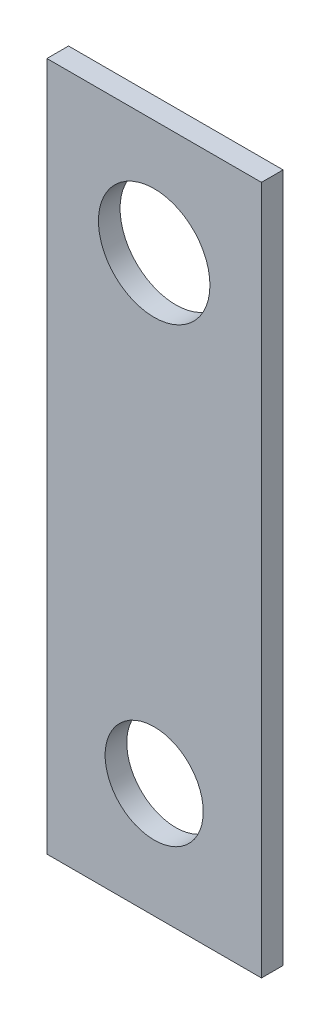
SolidWorks part; units mm, degrees
ref_plane "Front Plane" through (0, 0, 0) normal (0, 0, 1) x (1, 0, 0)
ref_plane "Top Plane" through (0, 0, 0) normal (0, 1, 0) x (1, 0, 0)
ref_plane "Right Plane" through (0, 0, 0) normal (1, 0, 0) x (0, 0, -1)
sketch "Sketch1" plane through (0, 0, 0) normal (0, 0, 1) x (1, 0, 0)
  line L0 (5.0419, -5.3975) -> (5.0419, -26.9875) construction
  line L1 (0, 0) -> (10.0838, 0)
  line L2 (0, 0) -> (0, -32.385)
  line L3 (0, -32.385) -> (10.0838, -32.385)
  line L4 (10.0838, 0) -> (10.0838, -32.385)
  circle A0 centre (5.0419, -5.3975) radius 2.6199
  circle A1 centre (5.0419, -26.9875) radius 2.3055
  point P9 (5.0419, -32.385)
  point P10 (5.0419, -16.1925)
  point P11 (10.0838, -16.1925)
  dimension "D1" = 10.0838
  dimension "D2" = 32.385
  dimension "D3" = 21.59
extrude "Boss-Extrude1" add sketch "Sketch1" along normal blind 1.016
